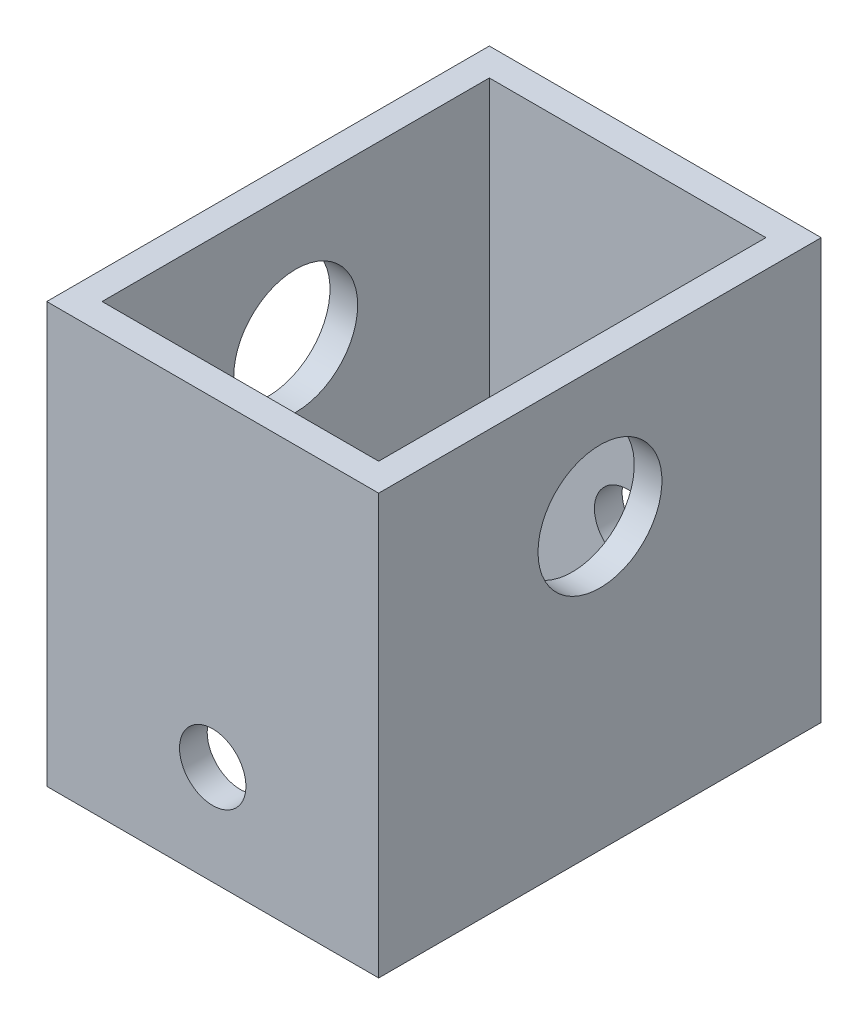
SolidWorks part; units mm, degrees
ref_plane "Front Plane" through (0, 0, 0) normal (0, 0, 1) x (1, 0, 0)
ref_plane "Top Plane" through (0, 0, 0) normal (0, 1, 0) x (1, 0, 0)
ref_plane "Right Plane" through (0, 0, 0) normal (1, 0, 0) x (0, 0, -1)
sketch "Sketch2" plane through (0, 0, 0) normal (0, 1, 0) x (1, 0, 0)
  line L1 (-38.1, 50.8) -> (38.1, 50.8)
  line L2 (-38.1, 50.8) -> (-38.1, -50.8)
  line L3 (-38.1, -50.8) -> (38.1, -50.8)
  line L4 (38.1, 50.8) -> (38.1, -50.8)
  line L5 (-38.1, 50.8) -> (38.1, -50.8) construction
  line L6 (-38.1, -50.8) -> (38.1, 50.8) construction
  point P0 (0, 0)
  dimension "D1" = 76.2
  dimension "D2" = 101.6
extrude "Extrude-Thin1" add sketch "Sketch2" along normal blind 96.393 thin
sketch "Sketch3" plane through (0, 0, -50.8) normal (0, 0, -1) x (-1, 0, 0)
  circle A0 centre (0, 22.86) radius 7.62
  dimension "D1" = 15.24
  dimension "D2" = 22.86
extrude "Cut-Extrude1" cut sketch "Sketch3" against normal through all
sketch "Sketch4" plane through (-38.1, 0, 0) normal (-1, 0, 0) x (0, 0, 1)
  line L0 (-44.45, 22.86) -> (-50.8, 22.86) construction
  circle A0 centre (0, 66.36) radius 14.224
  dimension "D1" = 28.448
  dimension "D2" = 43.5
extrude "Cut-Extrude2" cut sketch "Sketch4" against normal through all
